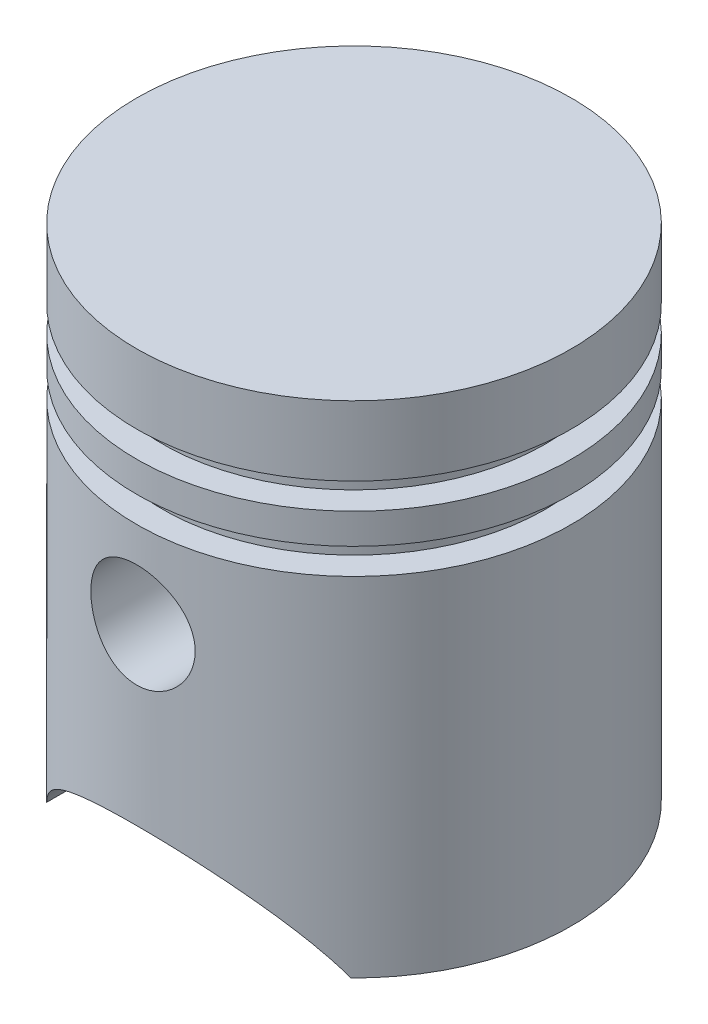
SolidWorks part; units mm, degrees
material "Plain Carbon Steel"
ref_plane "Front Plane" through (0, 0, 0) normal (0, 0, 1) x (1, 0, 0)
ref_plane "Top Plane" through (0, 0, 0) normal (0, 1, 0) x (1, 0, 0)
ref_plane "Right Plane" through (0, 0, 0) normal (1, 0, 0) x (0, 0, -1)
sketch "Sketch1" plane through (0, 0, 0) normal (0, 0, 1) x (1, 0, 0)
  line L0 (0, 63) -> (0, 61) construction
  line L1 (23, 0) -> (25, 0)
  line L2 (25, 0) -> (25, 40)
  line L3 (25, 40) -> (22, 40)
  line L4 (22, 40) -> (22, 43)
  line L5 (22, 43) -> (25, 43)
  line L6 (25, 43) -> (25, 46.5)
  line L7 (25, 46.5) -> (22, 46.5)
  line L8 (22, 46.5) -> (22, 49.5)
  line L9 (22, 49.5) -> (25, 49.5)
  line L10 (25, 49.5) -> (25, 57.5)
  line L11 (0, 0) -> (25, 0) construction
  line L12 (23, 56.2037) -> (0, 56.2037)
  line L13 (23, 0) -> (23, 38)
  line L14 (23, 38) -> (20, 38)
  line L15 (20, 38) -> (20, 44.75)
  line L16 (20, 44.75) -> (20, 44.75)
  line L17 (20, 44.75) -> (20, 44.75)
  line L18 (20, 44.75) -> (20, 44.75)
  line L19 (20, 44.75) -> (20, 51.5)
  line L20 (20, 51.5) -> (23, 51.5)
  line L21 (23, 51.5) -> (23, 56.2037)
  line L22 (23, 2) -> (23, 38) construction
  line L23 (2, 60.9622) -> (2, 2) construction
  line L24 (0, 63) -> (0, 0) construction
  line L25 (2, 2) -> (23, 2) construction
  line L26 (0, 56.2037) -> (0, 57.5)
  line L27 (0, 57.5) -> (25, 57.5)
  arc A0 (0, 63) -> (25, 57.5) centre (-0.095, 3.0001) cw construction
  arc A1 (0, 61) -> (23, 56.2037) centre (-0.095, 3.0001) cw construction
  arc A2 (2, 60.9622) -> (23, 56.2037) centre (-0.095, 3.0001) cw construction
  dimension "D7" = 60
  dimension "D1" = 23
  dimension "D2" = 40
  dimension "D4" = 3
  dimension "D5" = 3.5
  dimension "D6" = 8
  dimension "D8" = 2
revolve "Revolve1" add sketch "Sketch1" angle 360 about L0
sketch "Sketch2" plane through (0, 0, 0) normal (0, 0, 1) x (1, 0, 0)
  line L0 (-17.5, 0) -> (17.5, 0)
  line L1 (-25, 0) -> (25, 0) construction
  line L2 (0, 0) -> (0, 10) construction
  arc A0 (-17.5, 0) -> (17.5, 0) centre (0, -10.3125) cw
  dimension "D1" = 10
  dimension "D2" = 35
extrude "Cut-Extrude1" cut sketch "Sketch2" against normal mid plane 63
sketch "Sketch3" plane through (0, 0, 0) normal (0, 0, 1) x (1, 0, 0)
  line L0 (0, 30) -> (0, 57.5) construction
  line L1 (25, 57.5) -> (-25, 57.5) construction
  circle A0 centre (0, 30) radius 6
  dimension "D2" = 12
  dimension "D1" = 27.5
extrude "Cut-Extrude2" cut sketch "Sketch3" against normal mid plane 63
ref_plane "Plane1" through (0, 0, 10) normal (0, 0, 1) x (1, 0, 0)
sketch "Sketch4" plane through (0, 0, 10) normal (0, 0, 1) x (1, 0, 0)
  circle A0 centre (0, 30) radius 6 construction
  circle A1 centre (0, 30) radius 6
  circle A2 centre (0, 30) radius 7.5
  dimension "D1" = 1.5
extrude "Boss-Extrude1" add sketch "Sketch4" along normal up to next
mirror "Mirror1" about plane through (0, 0, 0) normal (0, 0, 1) of "Boss-Extrude1"
